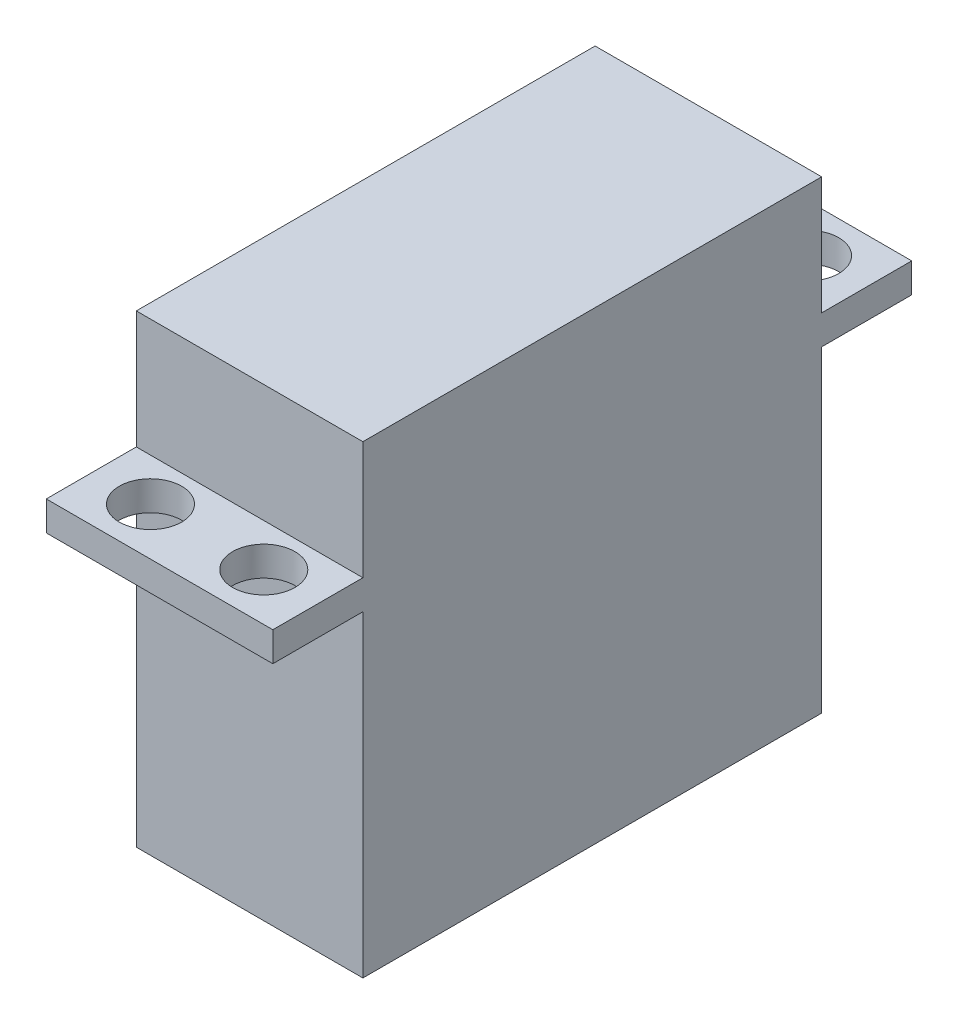
SolidWorks part; units mm, degrees
ref_plane "Front Plane" through (0, 0, 0) normal (0, 0, 1) x (1, 0, 0)
ref_plane "Top Plane" through (0, 0, 0) normal (0, 1, 0) x (1, 0, 0)
ref_plane "Right Plane" through (0, 0, 0) normal (1, 0, 0) x (0, 0, -1)
sketch "Sketch2" plane through (0, 0, 0) normal (0, 1, 0) x (1, 0, 0)
  line L1 (-10, -20.25) -> (10, -20.25)
  line L2 (-10, -20.25) -> (-10, 20.25)
  line L3 (-10, 20.25) -> (10, 20.25)
  line L4 (10, -20.25) -> (10, 20.25)
  line L5 (-10, -20.25) -> (10, 20.25) construction
  line L6 (-10, 20.25) -> (10, -20.25) construction
  point P0 (0, 0)
  point P6 (0, 533.3299)
  point P7 (0, 36.6049)
  dimension "D1" = 20
  dimension "D2" = 40.5
extrude "Boss-Extrude1" add sketch "Sketch2" along normal blind 41
ref_plane "Plane1" through (0, 28, 0) normal (0, 1, 0) x (1, 0, 0)
sketch "Sketch3" plane through (0, 28, 0) normal (0, 1, 0) x (1, 0, 0)
  line L0 (10, -20.25) -> (10, 20.25) construction
  line L1 (-10, -28.2) -> (10, -28.2)
  line L2 (-10, -28.2) -> (-10, 28.2)
  line L3 (-10, 28.2) -> (10, 28.2)
  line L4 (10, -28.2) -> (10, 28.2)
  line L5 (-10, -28.2) -> (10, 28.2) construction
  line L6 (-10, 28.2) -> (10, -28.2) construction
  point P0 (0, 0)
  dimension "D1" = 56.4
extrude "Boss-Extrude2" add sketch "Sketch3" along normal blind 2.6
sketch "Sketch5" plane through (0, 28, 0) normal (0, 1, 0) x (1, 0, 0)
  line L1 (-5, -24) -> (5, -24) construction
  line L2 (-5, -24) -> (-5, 24) construction
  line L3 (-5, 24) -> (5, 24) construction
  line L4 (5, -24) -> (5, 24) construction
  line L5 (-5, -24) -> (5, 24) construction
  line L6 (-5, 24) -> (5, -24) construction
  point P0 (0, 0)
  point P7 (-5, 24)
  point P8 (5, 24)
  point P9 (5, -24)
  point P10 (-5, -24)
  dimension "D1" = 48
  dimension "D2" = 10
hole_wizard "M5 Clearance Hole1" positions "Sketch6" profile "Sketch8" hole size "M5" standard "ANSI Metric" end condition through all
sketch "Sketch6" plane through (0, 30.6, 0) normal (0, 1, 0) x (1, 0, 0)
  point P0 (-5, 24)
  point P4 (5, 24)
  point P7 (5, -24)
  point P10 (-5, -24)
sketch "Sketch8" plane through (-5, 30.6, -24) normal (1, 0, 0) x (0, 0, 1)
  line L0 (0, 0) -> (0, 30.6)
  line L1 (0, 30.6) -> (2.75, 30.6)
  line L2 (2.75, 30.6) -> (2.75, 0)
  line L5 (2.75, 0) -> (0, 0)
  line L11 (0, -6.35) -> (0, 107.95) construction
  dimension "Thru Hole Dia." = 5.5
  dimension "Thru Hole Depth" = 30.6
